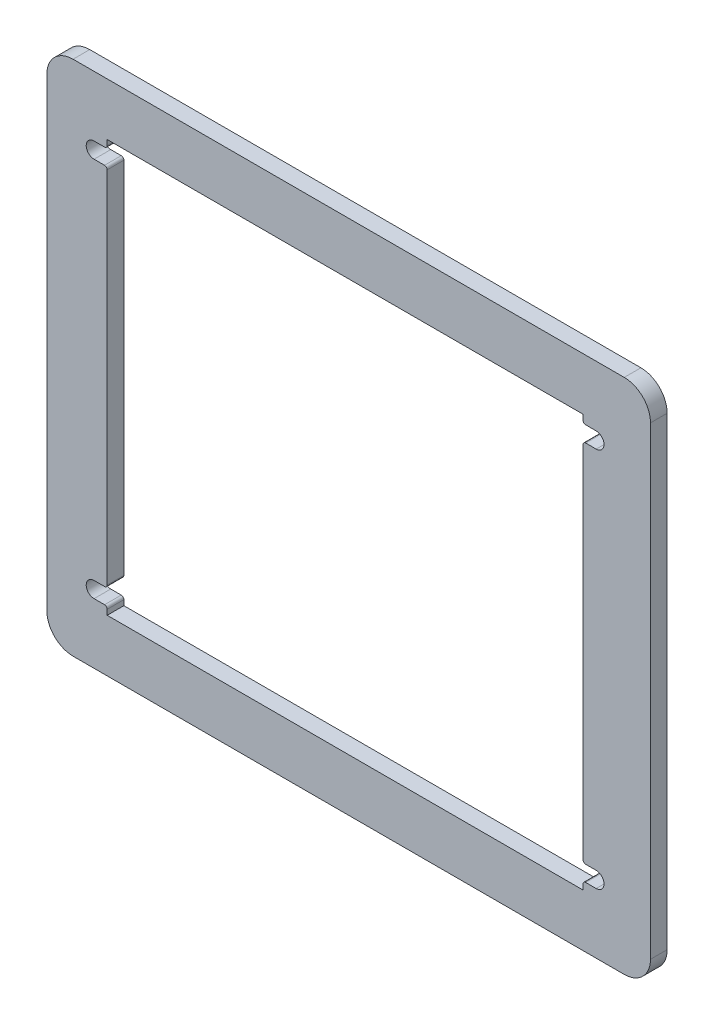
SolidWorks part; units mm, degrees
material "PMMA"
ref_plane "Front Plane" through (0, 0, 0) normal (0, 0, 1) x (1, 0, 0)
ref_plane "Top Plane" through (0, 0, 0) normal (0, 1, 0) x (1, 0, 0)
ref_plane "Right Plane" through (0, 0, 0) normal (1, 0, 0) x (0, 0, -1)
sketch "Sketch2" plane through (0, 0, 0) normal (0, 0, 1) x (1, 0, 0)
  line L0 (50.8246, 0) -> (50.8246, -78.5) construction
  line L1 (0, 0) -> (103, 0) construction
  line L2 (0, 0) -> (0, -78.5) construction
  line L3 (0, -78.5) -> (103, -78.5) construction
  line L4 (103, 0) -> (103, -78.5) construction
  line L5 (5.5, 0) -> (5.5, -1)
  line L6 (-1, 10) -> (104, 10)
  line L7 (-6, 5) -> (-6, -83.5)
  line L8 (-1, -88.5) -> (104, -88.5)
  line L9 (109, 5) -> (109, -83.5)
  line L10 (5.5, -78.5) -> (96.1492, -78.5)
  line L11 (5.5, 0) -> (96.1492, 0)
  line L12 (96.1492, 0) -> (96.1492, -1)
  line L13 (3, -1.5) -> (5, -1.5)
  line L14 (3, -4.5) -> (5, -4.5)
  line L15 (5.5, -5) -> (5.5, -73.5)
  line L16 (3, -77) -> (5, -77)
  line L17 (3, -74) -> (5, -74)
  line L18 (5.5, -77.5) -> (5.5, -78.5)
  line L19 (98.6492, -4.5) -> (96.6492, -4.5)
  line L20 (98.6492, -1.5) -> (96.6492, -1.5)
  line L21 (96.1492, -5) -> (96.1492, -73.5)
  line L22 (98.6492, -74) -> (96.6492, -74)
  line L23 (98.6492, -77) -> (96.6492, -77)
  line L24 (96.1492, -77.5) -> (96.1492, -78.5)
  arc A0 (3, -1.5) -> (3, -4.5) centre (3, -3) ccw
  arc A1 (3, -74) -> (3, -77) centre (3, -75.5) ccw
  arc A2 (98.6492, -74) -> (98.6492, -77) centre (98.6492, -75.5) cw
  arc A3 (98.6492, -1.5) -> (98.6492, -4.5) centre (98.6492, -3) cw
  arc A4 (-1, 10) -> (-6, 5) centre (-1, 5) ccw
  arc A5 (-6, -83.5) -> (-1, -88.5) centre (-1, -83.5) ccw
  arc A6 (109, -83.5) -> (104, -88.5) centre (104, -83.5) cw
  arc A7 (109, 5) -> (104, 10) centre (104, 5) ccw
  arc A8 (5.5, -1) -> (5, -1.5) centre (5, -1) cw
  arc A9 (5.5, -5) -> (5, -4.5) centre (5, -5) ccw
  arc A10 (5.5, -73.5) -> (5, -74) centre (5, -73.5) cw
  arc A11 (5.5, -77.5) -> (5, -77) centre (5, -77.5) ccw
  arc A12 (96.1492, -73.5) -> (96.6492, -74) centre (96.6492, -73.5) ccw
  arc A13 (96.1492, -77.5) -> (96.6492, -77) centre (96.6492, -77.5) cw
  arc A14 (96.1492, -1) -> (96.6492, -1.5) centre (96.6492, -1) ccw
  arc A15 (96.1492, -5) -> (96.6492, -4.5) centre (96.6492, -5) cw
  point P24 (50.8246, 0)
  point P25 (50.8246, -78.5)
  point P47 (5.5, -1.5)
  point P50 (5.5, -4.5)
  point P53 (5.5, -74)
  point P56 (5.5, -77)
  point P61 (96.1492, -77)
  point P66 (96.1492, -4.5)
  dimension "D5" = 3
  dimension "D6" = 3
  dimension "D16" = 5
  dimension "D17" = 5
  dimension "D18" = 5
  dimension "D19" = 5
  dimension "D20" = 0.5
  dimension "D21" = 0.5
  dimension "D22" = 0.5
  dimension "D23" = 0.5
  dimension "D24" = 0.5
  dimension "D25" = 0.5
  dimension "D26" = 0.5
  dimension "D27" = 0.5
  dimension "D1" = 103
  dimension "D2" = 78.5
  dimension "D3" = 3
  dimension "D4" = 3
  dimension "D7" = 3
  dimension "D8" = 3
  dimension "D9" = 2.5
  dimension "D10" = 6
  dimension "D11" = 10
  dimension "D12" = 10
  dimension "D13" = 0
  dimension "D14" = 0
  dimension "D15" = 6
extrude "Boss-Extrude1" add sketch "Sketch2" along normal blind 3.175
